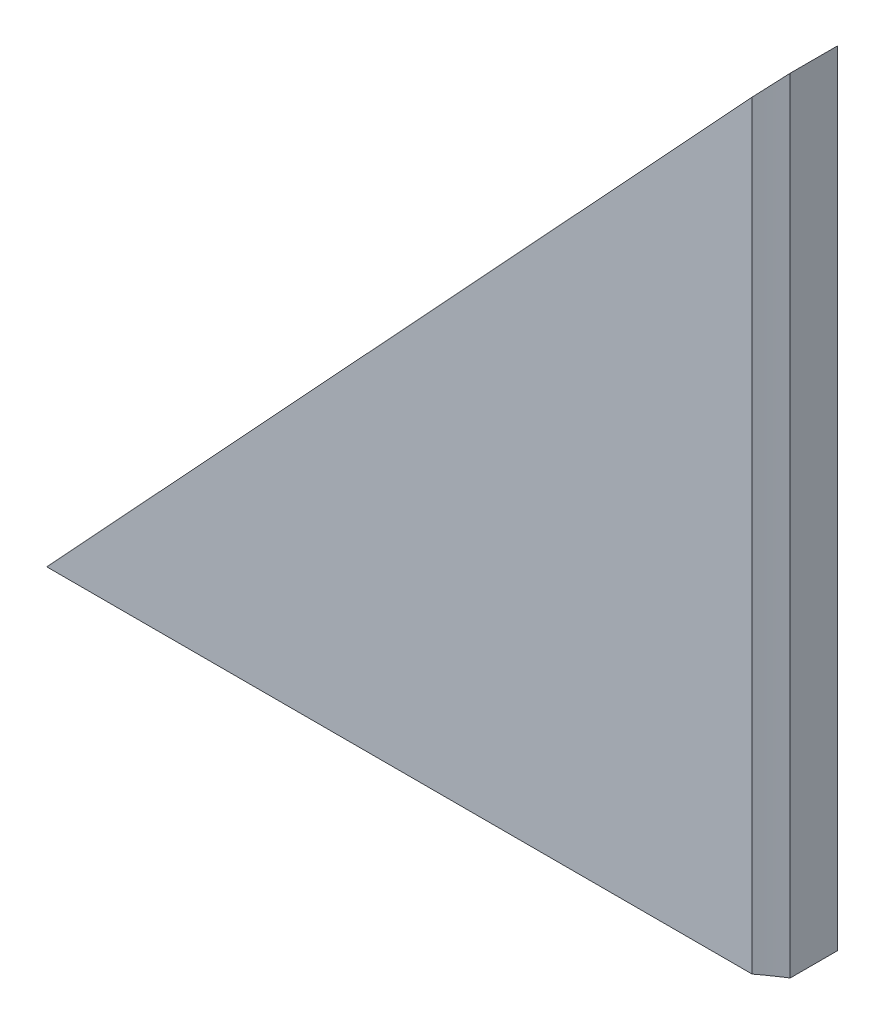
SolidWorks part; units mm, degrees
ref_plane "Płaszczyzna przednia" through (0, 0, 0) normal (0, 0, 1) x (1, 0, 0)
ref_plane "Płaszczyzna górna" through (0, 0, 0) normal (0, 1, 0) x (1, 0, 0)
ref_plane "Płaszczyzna prawa" through (0, 0, 0) normal (1, 0, 0) x (0, 0, -1)
ref_plane "Płaszczyzna1" through (0, 0, -1.5) normal (0, 0, -1) x (-1, 0, 0)
sketch "Szkic1" plane through (0, 0, -1.5) normal (0, 0, -1) x (-1, 0, 0)
  line L1 (23.22, 0) -> (0, 25)
  line L2 (0, 25) -> (0, 0)
  line L3 (0, 0) -> (23.22, 0)
  dimension "D1" = 23.22
  dimension "D2" = 25
extrude "Dodanie-wyciągnięcie1" add sketch "Szkic1" against normal blind 2
sketch "Szkic2" plane through (0, 0, 0) normal (0, -1, 0) x (-1, 0, 0)
  circle A0 centre (-6.78, -10.5015) radius 12.5
  dimension "D1" = 25
  dimension "D2" = 30
  dimension "D3" = 12.0015
extrude "Wytnij-wyciągnięcie1" cut sketch "Szkic2" against normal blind 25
